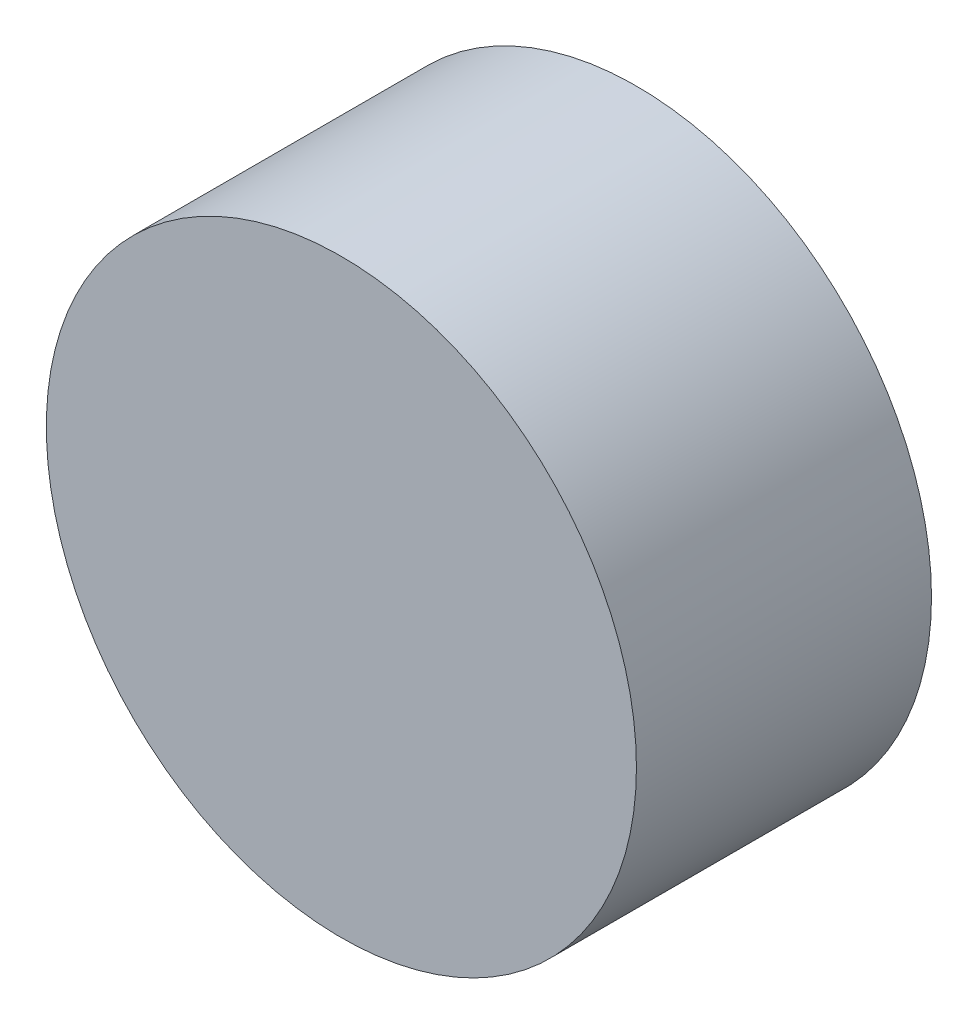
SolidWorks part; units mm, degrees
ref_plane "前基準面" through (0, 0, 0) normal (0, 0, 1) x (1, 0, 0)
ref_plane "上基準面" through (0, 0, 0) normal (0, 1, 0) x (1, 0, 0)
ref_plane "右基準面" through (0, 0, 0) normal (1, 0, 0) x (0, 0, -1)
sketch "草圖1" plane through (0, 0, 0) normal (0, 0, 1) x (1, 0, 0)
  circle A0 centre (0, 0) radius 30
  dimension "D1" = 60
extrude "填料-伸長1" add sketch "草圖1" along normal blind 30
